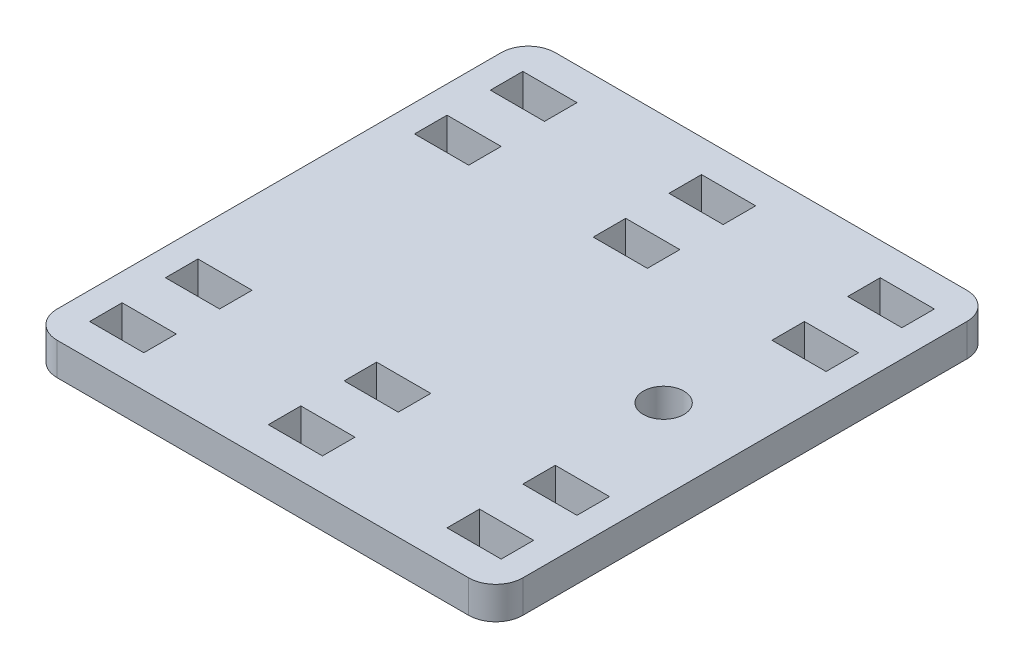
SolidWorks part; units mm, degrees
material "Maple"
ref_plane "Front Plane" through (0, 0, 0) normal (0, 0, 1) x (1, 0, 0)
ref_plane "Top Plane" through (0, 0, 0) normal (0, 1, 0) x (1, 0, 0)
ref_plane "Right Plane" through (0, 0, 0) normal (1, 0, 0) x (0, 0, -1)
sketch "Sketch1" plane through (0, 0, 0) normal (0, 1, 0) x (1, 0, 0)
  line L0 (86, -161.1) -> (86, 120.4) construction
  line L1 (0, 0) -> (86, 0)
  line L2 (0, 0) -> (0, 92)
  line L3 (0, 92) -> (86, 92)
  line L4 (86, 0) -> (86, 92)
  dimension "D2" = 92
extrude "Boss-Extrude1" add sketch "Sketch1" along normal blind 6
ref_plane "Plane1" through (0, 3, 0) normal (0, 1, 0) x (1, 0, 0)
ref_plane "Plane2" through (0, 0, -46) normal (0, 0, 1) x (1, 0, 0)
hole_wizard "Ø7.5 (7.5) Diameter Hole1" positions "Sketch3" profile "Sketch2" hole size "Ø7.5" standard "ANSI Metric" end condition through all
sketch "Sketch3" plane through (0, 6, 0) normal (0, 1, 0) x (1, 0, 0)
  circle A0 centre (71, 46) radius 4 construction
  point P0 (71, 46)
sketch "Sketch2" plane through (71, 6, -46) normal (1, 0, 0) x (0, 0, 1)
  line L0 (0, 0) -> (0, 6)
  line L1 (0, 6) -> (3.75, 6)
  line L2 (3.75, 6) -> (3.75, 0)
  line L5 (3.75, 0) -> (0, 0)
  line L11 (0, -6.35) -> (0, 107.95) construction
  dimension "Thru Hole Dia." = 7.5
  dimension "Thru Hole Depth" = 6
sketch "Sketch4" plane through (0, 0, 0) normal (0, -1, 0) x (1, 0, 0)
  line L0 (0, -9) -> (86, -9) construction
  line L1 (0, -92) -> (0, 0) construction
  line L2 (86, 0) -> (86, -92) construction
  line L3 (25.85, -9) -> (-25.85, -9) construction
  line L4 (10, -9) -> (43, -9) construction
  line L5 (0, -23) -> (86, -23) construction
  line L6 (11, -23) -> (-11, -23) construction
  line L7 (10, -23) -> (43, -23) construction
  point P8 (10, -9)
  point P11 (43, -9)
  point P12 (76, -9)
  point P17 (10, -23)
  point P19 (43, -23)
  point P20 (76, -23)
  dimension "D2" = 10
  dimension "D3" = 10
  dimension "D5" = 10
  dimension "D6" = 10
  dimension "D1" = 3
  dimension "D4" = 3
sketch "Sketch6" plane through (9.2322, 3, 35) normal (0, -1, 0) x (1, 0, 0)
  line L1 (-4.2322, -41) -> (5.7678, -41)
  line L2 (-4.2322, -41) -> (-4.2322, -47)
  line L3 (-4.2322, -47) -> (5.7678, -47)
  line L4 (5.7678, -41) -> (5.7678, -47)
  line L5 (-4.2322, -41) -> (5.7678, -47) construction
  line L6 (-4.2322, -47) -> (5.7678, -41) construction
  point P0 (0.7678, -44)
  dimension "D1" = 10
  dimension "D2" = 6
extrude "Cut-Extrude1" cut sketch "Sketch6" against normal through all and the other way through all
other "Smart-Feature1<virtual_pin-24>"
sketch "Sketch61" plane through (42.2322, 3, 35) normal (0, -1, 0) x (1, 0, 0)
  line L1 (-4.2322, -41) -> (5.7678, -41)
  line L2 (-4.2322, -41) -> (-4.2322, -47)
  line L3 (-4.2322, -47) -> (5.7678, -47)
  line L4 (5.7678, -41) -> (5.7678, -47)
  line L5 (-4.2322, -41) -> (5.7678, -47) construction
  line L6 (-4.2322, -47) -> (5.7678, -41) construction
  point P0 (0.7678, -44)
  dimension "D1" = 10
  dimension "D2" = 6
extrude "Cut-Extrude11" cut sketch "Sketch61" against normal through all and the other way through all
other "Smart-Feature2<virtual_pin-25>"
sketch "Sketch62" plane through (75.2322, 3, 35) normal (0, -1, 0) x (1, 0, 0)
  line L1 (-4.2322, -41) -> (5.7678, -41)
  line L2 (-4.2322, -41) -> (-4.2322, -47)
  line L3 (-4.2322, -47) -> (5.7678, -47)
  line L4 (5.7678, -41) -> (5.7678, -47)
  line L5 (-4.2322, -41) -> (5.7678, -47) construction
  line L6 (-4.2322, -47) -> (5.7678, -41) construction
  point P0 (0.7678, -44)
  dimension "D1" = 10
  dimension "D2" = 6
extrude "Cut-Extrude12" cut sketch "Sketch62" against normal through all and the other way through all
other "Smart-Feature3<virtual_pin-26>"
sketch "Sketch64" plane through (9.2322, 3, 21) normal (0, -1, 0) x (1, 0, 0)
  line L1 (-4.2322, -41) -> (5.7678, -41)
  line L2 (-4.2322, -41) -> (-4.2322, -47)
  line L3 (-4.2322, -47) -> (5.7678, -47)
  line L4 (5.7678, -41) -> (5.7678, -47)
  line L5 (-4.2322, -41) -> (5.7678, -47) construction
  line L6 (-4.2322, -47) -> (5.7678, -41) construction
  point P0 (0.7678, -44)
  dimension "D1" = 10
  dimension "D2" = 6
extrude "Cut-Extrude14" cut sketch "Sketch64" against normal through all and the other way through all
other "Smart-Feature1<virtual_pin-27>"
sketch "Sketch65" plane through (42.2322, 3, 21) normal (0, -1, 0) x (1, 0, 0)
  line L1 (-4.2322, -41) -> (5.7678, -41)
  line L2 (-4.2322, -41) -> (-4.2322, -47)
  line L3 (-4.2322, -47) -> (5.7678, -47)
  line L4 (5.7678, -41) -> (5.7678, -47)
  line L5 (-4.2322, -41) -> (5.7678, -47) construction
  line L6 (-4.2322, -47) -> (5.7678, -41) construction
  point P0 (0.7678, -44)
  dimension "D1" = 10
  dimension "D2" = 6
extrude "Cut-Extrude15" cut sketch "Sketch65" against normal through all and the other way through all
other "Smart-Feature2<virtual_pin-28>"
sketch "Sketch66" plane through (75.2322, 3, 21) normal (0, -1, 0) x (1, 0, 0)
  line L1 (-4.2322, -41) -> (5.7678, -41)
  line L2 (-4.2322, -41) -> (-4.2322, -47)
  line L3 (-4.2322, -47) -> (5.7678, -47)
  line L4 (5.7678, -41) -> (5.7678, -47)
  line L5 (-4.2322, -41) -> (5.7678, -47) construction
  line L6 (-4.2322, -47) -> (5.7678, -41) construction
  point P0 (0.7678, -44)
  dimension "D1" = 10
  dimension "D2" = 6
extrude "Cut-Extrude16" cut sketch "Sketch66" against normal through all and the other way through all
other "Smart-Feature3<virtual_pin-29>"
mirror "Mirror1" about plane through (0, 0, -46) normal (0, 0, 1) of "Cut-Extrude1", "Cut-Extrude11", "Cut-Extrude12", "Cut-Extrude16", "Cut-Extrude15", "Cut-Extrude14"
fillet "Fillet1" radius 5 4 edges at (86, 3, -92) (86, 3, 0) (0, 3, 0) (0, 3, -92)
